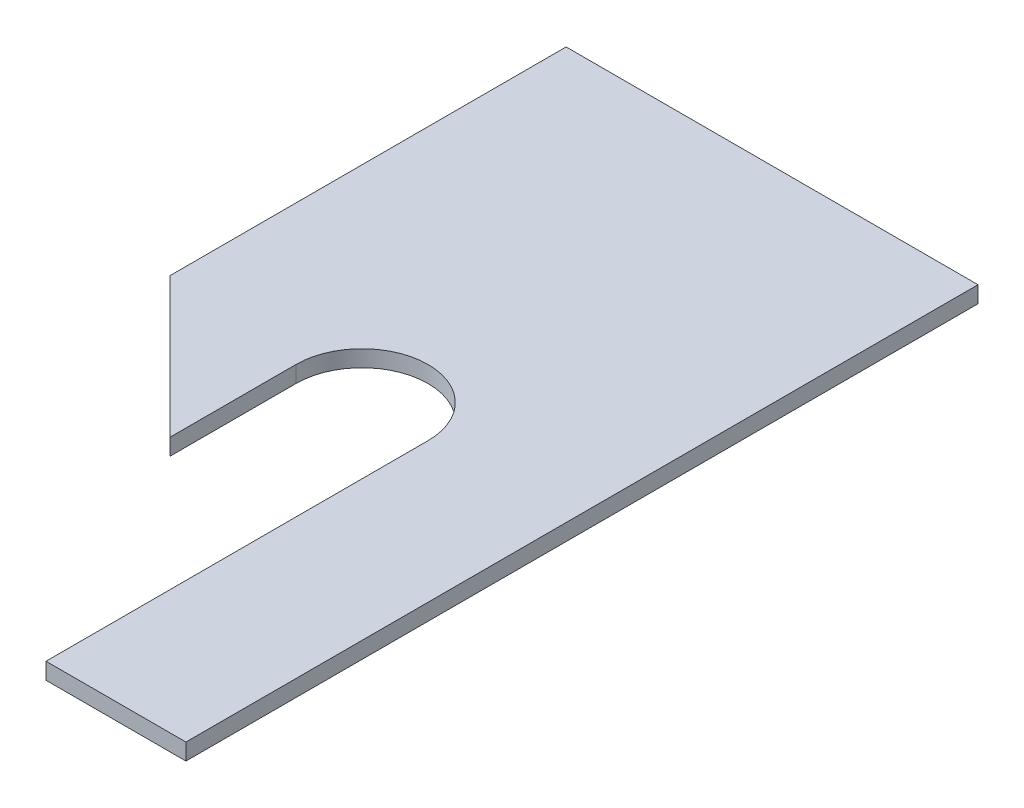
SolidWorks part; units mm, degrees
material "ABS PC"
ref_plane "Front Plane" through (0, 0, 0) normal (0, 0, 1) x (1, 0, 0)
ref_plane "Top Plane" through (0, 0, 0) normal (0, 1, 0) x (1, 0, 0)
ref_plane "Right Plane" through (0, 0, 0) normal (1, 0, 0) x (0, 0, -1)
sketch "Sketch1" plane through (0, 0, 0) normal (0, 1, 0) x (1, 0, 0)
  line L1 (-19.812, 0) -> (19.812, 0)
  line L2 (-19.812, 0) -> (-19.812, -63.5)
  line L3 (-19.812, -63.5) -> (19.812, -63.5)
  line L4 (19.812, 0) -> (19.812, -63.5)
  dimension "D1" = 19.812
  dimension "D2" = 63.5
extrude "Boss-Extrude1" add sketch "Sketch1" along normal blind 1.5875
sketch "Sketch2" plane through (0, 0, 0) normal (0, -1, 0) x (1, 0, 0)
  line L0 (-19.812, 0) -> (-19.812, 63.5) construction
  line L1 (19.812, 0) -> (-19.812, 0)
  line L2 (19.812, 0) -> (19.812, 3.175)
  line L3 (19.812, 3.175) -> (-19.812, 3.175)
  line L4 (-19.812, 0) -> (-19.812, 3.175)
  dimension "D1" = 3.175
extrude "Boss-Extrude2" add sketch "Sketch2" along normal blind 6.35
extrude "Cut-Extrude1" cut sketch "Sketch3" against normal through all
sketch "Sketch3" plane through (10.2893, 1.5875, 36.0694) normal (0, 1, 0) x (1, 0, 0)
  circle A0 centre (-10.2893, -3.3796) radius 6.35
sketch "Sketch4" plane through (0, 1.5875, 0) normal (0, 1, 0) x (1, 0, 0)
  line L0 (-19.812, -38.1) -> (5.588, -63.5)
  line L1 (-19.812, 0) -> (-19.812, -63.5) construction
  line L2 (-19.812, -63.5) -> (19.812, -63.5) construction
  line L3 (-19.812, -63.5) -> (5.588, -63.5)
  line L4 (-19.812, -38.1) -> (-19.812, -63.5)
  dimension "D1" = 45
  dimension "D2" = 25.4
extrude "Cut-Extrude2" cut sketch "Sketch4" against normal through all and the other way through all
sketch "Sketch5" plane through (0, 1.5875, 0) normal (0, 1, 0) x (1, 0, 0)
  line L1 (-6.35, -39.449) -> (6.35, -39.449)
  line L2 (-6.35, -39.449) -> (-6.35, -68.3957)
  line L3 (-6.35, -68.3957) -> (6.35, -68.3957)
  line L4 (6.35, -39.449) -> (6.35, -68.3957)
  circle A0 centre (0, -39.449) radius 6.35 construction
  point P6 (0, 0)
  point P7 (-6.35, -68.3957)
  point P10 (0, -39.449)
extrude "Cut-Extrude3" cut sketch "Sketch5" against normal through all
sketch "Sketch6" plane through (0, 1.5875, 0) normal (0, 1, 0) x (1, 0, 0)
  line L1 (19.812, -63.5) -> (6.35, -63.5)
  line L2 (19.812, -63.5) -> (19.812, -76.2)
  line L3 (19.812, -76.2) -> (6.35, -76.2)
  line L4 (6.35, -63.5) -> (6.35, -76.2)
  dimension "D1" = 12.7
extrude "Boss-Extrude3" add sketch "Sketch6" against normal up to surface (1.5875 mm away) up to face at (0, 0, 36.945)
sketch "Sketch7" plane through (0, 0, 0) normal (0, 0, -1) x (-1, 0, 0)
  line L1 (-19.812, -6.35) -> (-12.7, -6.35)
  line L2 (-19.812, -6.35) -> (-19.812, 0)
  line L3 (-19.812, 0) -> (-12.7, 0)
  line L4 (-12.7, -6.35) -> (-12.7, 0)
  line L5 (19.812, -6.35) -> (12.7, -6.35)
  line L6 (19.812, -6.35) -> (19.812, 0)
  line L7 (19.812, 0) -> (12.7, 0)
  line L8 (12.7, -6.35) -> (12.7, 0)
  line L9 (-19.812, 0) -> (-6.35, 0) construction
  dimension "D1" = 25.4
extrude "Cut-Extrude4" cut sketch "Sketch7" against normal through all
fillet "Fillet1" radius 3.175 3 edges at (0, 0, 3.175) (-12.7, 0, 1.5875) (12.7, 0, 1.5875)
hole_wizard "#4 Clearance Hole1" positions "Sketch8" profile "Sketch9" hole size "#4" standard "ANSI Inch" end condition through all
sketch "Sketch8" plane through (0, 0, 0) normal (0, 0, -1) x (-1, 0, 0)
  line L0 (-9.525, -3.175) -> (0, 0)
  line L1 (0, 0) -> (9.525, -3.175)
  line L4 (12.7, -6.35) -> (-12.7, -6.35) construction
  point P0 (-9.525, -3.175)
  point P2 (9.525, -3.175)
  dimension "D1" = 19.05
  dimension "D2" = 3.175
sketch "Sketch9" plane through (9.525, -3.175, 0) normal (1, 0, 0) x (0, 1, 0)
  line L0 (0, 0) -> (0, 76.2)
  line L1 (0, 76.2) -> (1.4732, 76.2)
  line L2 (1.4732, 76.2) -> (1.4732, 0)
  line L5 (1.4732, 0) -> (0, 0)
  line L11 (0, -6.35) -> (0, 107.95) construction
  dimension "Thru Hole Dia." = 2.9464
  dimension "Thru Hole Depth" = 76.2
sketch "Sketch10" plane through (0, 0, 3.175) normal (0, 0, 1) x (1, 0, 0)
  circle A0 centre (9.525, -3.175) radius 2.3813
  circle A1 centre (-9.525, -3.175) radius 2.3813
  dimension "D1" = 4.7625
extrude "Cut-Extrude5" cut sketch "Sketch10" along normal through all
